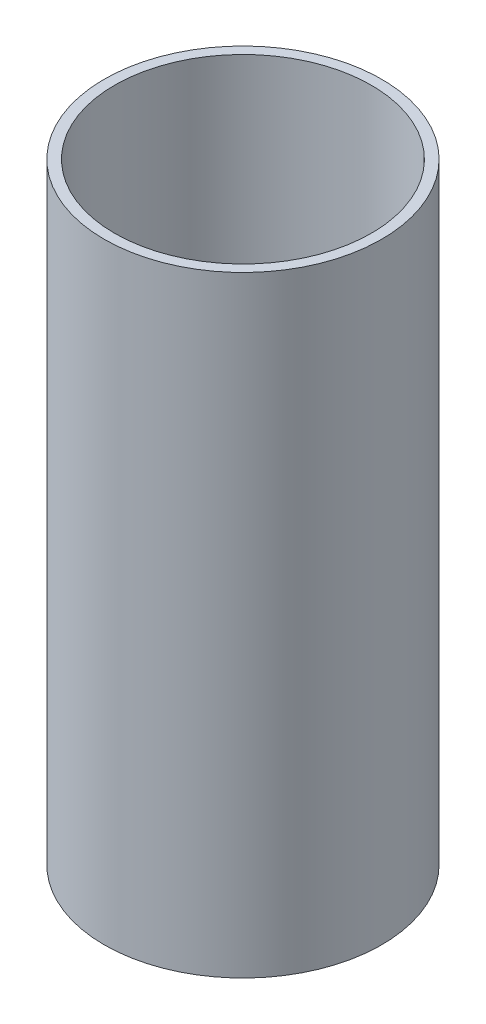
SolidWorks part; units mm, degrees
ref_plane "Front Plane" through (0, 0, 0) normal (0, 0, 1) x (1, 0, 0)
ref_plane "Top Plane" through (0, 0, 0) normal (0, 1, 0) x (1, 0, 0)
ref_plane "Right Plane" through (0, 0, 0) normal (1, 0, 0) x (0, 0, -1)
sketch "Sketch1" plane through (0, 0, 0) normal (0, 1, 0) x (1, 0, 0)
  circle A0 centre (0, 0) radius 109.5375
  circle A1 centre (0, 0) radius 101.3587
  dimension "D1" = 219.075
  dimension "D2" = 202.7174
extrude "Extrude1" add sketch "Sketch1" along normal mid plane 482.6
equation "\"D2@Sketch1\" = \"D1@Sketch1\" - .322*2"
